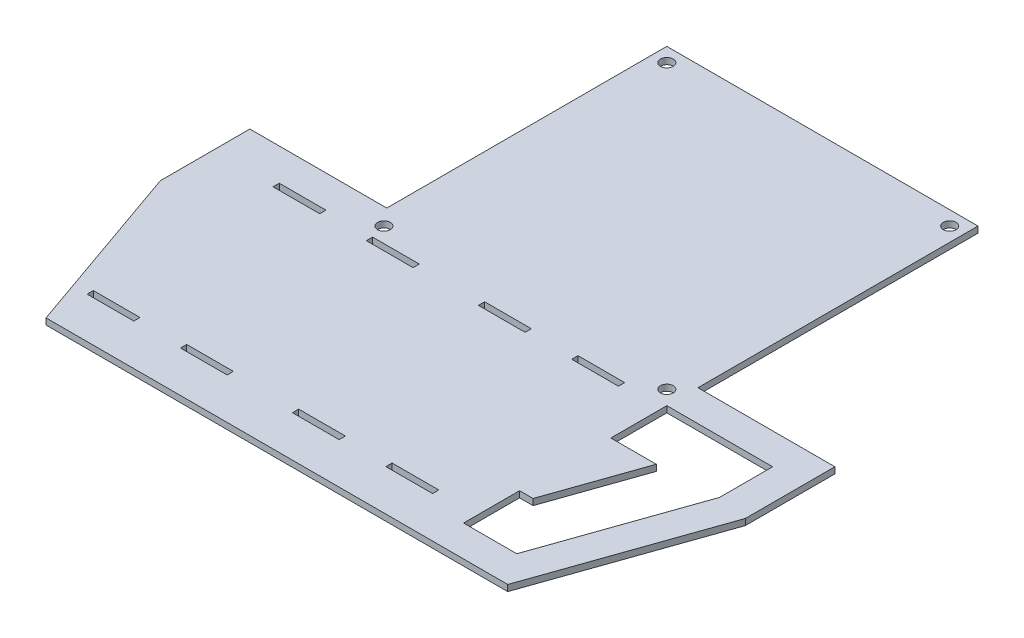
SolidWorks part; units mm, degrees
other "Marca1"
sketch "Croquis6" plane through (-94, 2, 114.9827) normal (0, 1, 0) x (-1, 0, 0)
ref_plane "Alzado" through (0, 0, 0) normal (0, 0, 1) x (1, 0, 0)
ref_plane "Planta" through (0, 0, 0) normal (0, 1, 0) x (1, 0, 0)
ref_plane "Vista lateral" through (0, 0, 0) normal (1, 0, 0) x (0, 0, -1)
sketch "Croquis1" plane through (0, 0, 0) normal (0, 1, 0) x (1, 0, 0)
  line L1 (50, -50) -> (-50, -50) construction
  line L2 (50, -55) -> (50, 50)
  line L3 (50, 50) -> (-50, 50)
  line L4 (-50, -55) -> (-50, 50)
  line L5 (50, -50) -> (-50, 50) construction
  line L6 (50, 50) -> (-50, -50) construction
  line L7 (50, -40) -> (100, -40) construction
  line L8 (74.1939, -125.32) -> (-74.1939, -125.32)
  line L10 (94, -68.7685) -> (94, -40) construction
  line L11 (-50, -55) -> (50, -55) construction
  line L16 (0, 50) -> (0, -114.9827) construction
  line L17 (40, -40) -> (94, -40)
  line L18 (94, -40) -> (94, -68.7685)
  line L19 (-40, -40) -> (-94, -40)
  line L20 (-94, -40) -> (-94, -68.7685)
  line L22 (-50, -40) -> (-100, -40) construction
  line L23 (74.1939, -125.32) -> (94, -68.7685)
  line L24 (-74.1939, -125.32) -> (-94, -68.7685)
  point P0 (0, 0)
  point P7 (0, 0)
  point P10 (0, 0)
  dimension "D1" = 100
  dimension "D2" = 100
  dimension "D3" = 175.32
extrude "Saliente-Extruir1" add sketch "Croquis1" along normal blind 2
sketch "Croquis2" plane through (0, 2, 0) normal (0, 1, 0) x (1, 0, 0)
  line L0 (0, -115) -> (0, 50) construction
  line L1 (50, 50) -> (-50, 50) construction
  line L3 (-50, 0) -> (50, 0) construction
  line L5 (-50, -40) -> (-50, 50) construction
  line L7 (50, -50) -> (-50, -50) construction
  circle A0 centre (-45.45, -45.45) radius 2.05
  circle A1 centre (45.45, -45.45) radius 2.05
  circle A2 centre (-45.45, 45.45) radius 2.05
  circle A3 centre (45.45, 45.45) radius 2.05
  dimension "D1" = 4.1
  dimension "D2" = 4.55
  dimension "D3" = 100
  dimension "D4" = 4.55
  dimension "D5" = 50
  dimension "D6" = 90.9
extrude "Cortar-Extruir1" cut sketch "Croquis2" against normal through all
sketch "Croquis4" plane through (0, 2, 0) normal (0, 1, 0) x (1, 0, 0)
  line L16 (50, -68) -> (64.6015, -68)
  line L17 (64.6015, -68) -> (64.6015, -68)
  line L25 (64.6015, -68) -> (54.3328, -97.32)
  line L26 (54.3328, -97.32) -> (50, -97.32)
  line L27 (67.1006, -115.32) -> (-74.1939, -115.32)
  line L28 (50, -50) -> (84, -50)
  line L29 (84, -50) -> (84, -67.0679)
  line L30 (84, -67.0679) -> (67.1006, -115.32)
  line L31 (67.1006, -115.32) -> (50, -115.32)
  line L32 (50, -50) -> (84, -50)
  line L33 (84, -50) -> (84, -67.0679)
  line L34 (84, -67.0679) -> (67.1006, -115.32)
  line L35 (50, -68) -> (50, -50)
  line L37 (67.1006, -115.32) -> (-74.1939, -115.32) construction
  line L38 (54.3328, -97.32) -> (-74.1939, -97.32) construction
  line L39 (50, -97.32) -> (50, -115.32)
  dimension "D1" = 10
  dimension "D2" = 18
  dimension "D3" = 4.3328
extrude "Cortar-Extruir3" cut sketch "Croquis4" against normal up to next
sketch "Croquis5" plane through (0, 2, 0) normal (0, 1, 0) x (1, 0, 0)
  line L0 (74.1939, -125.32) -> (-74.1939, -125.32) construction
  line L1 (-74.1939, -107.2327) -> (36.8061, -107.2327) construction
  line L2 (-74.1939, -55.2327) -> (36.8061, -55.2327) construction
  line L3 (74.1939, -125.32) -> (-74.1939, -125.32) construction
  line L4 (-74.1939, -107.2327) -> (36.8061, -107.2327) construction
  line L5 (-74.1939, -55.2327) -> (36.8061, -55.2327) construction
  line L6 (45.45, -47.5) -> (-45.45, -47.5) construction
  line L7 (36.8061, -55.2327) -> (36.8061, -47.5) construction
  line L8 (36.8061, -50.3577) -> (21.8061, -50.3577)
  line L9 (36.8061, -50.3577) -> (36.8061, -52.3577)
  line L10 (36.8061, -52.3577) -> (21.8061, -52.3577)
  line L11 (21.8061, -50.3577) -> (21.8061, -52.3577)
  line L12 (36.8061, -51.3577) -> (-74.1865, -51.3577) construction
  line L13 (-18.6939, -55.2327) -> (-18.6939, -47.5) construction
  line L14 (-74.1939, -50.3577) -> (-59.1939, -50.3577)
  line L15 (-74.1939, -50.3577) -> (-74.1939, -52.3577)
  line L16 (-74.1939, -52.3577) -> (-59.1939, -52.3577)
  line L17 (-59.1939, -50.3577) -> (-59.1939, -52.3577)
  line L18 (-44.1939, -50.3577) -> (-29.1939, -50.3577)
  line L19 (-44.1939, -50.3577) -> (-44.1939, -52.3577)
  line L20 (-44.1939, -52.3577) -> (-29.1939, -52.3577)
  line L21 (-29.1939, -50.3577) -> (-29.1939, -52.3577)
  line L22 (-8.1939, -50.3577) -> (6.8061, -50.3577)
  line L23 (-8.1939, -50.3577) -> (-8.1939, -52.3577)
  line L24 (-8.1939, -52.3577) -> (6.8061, -52.3577)
  line L25 (6.8061, -50.3577) -> (6.8061, -52.3577)
  line L26 (-74.1939, -55.2327) -> (-74.1939, -81.2327) construction
  line L27 (36.8061, -81.2327) -> (-74.1939, -81.2327) construction
  line L28 (-74.1939, -110.1077) -> (-59.1939, -110.1077)
  line L29 (-59.1939, -112.1077) -> (-59.1939, -110.1077)
  line L30 (-74.1939, -112.1077) -> (-59.1939, -112.1077)
  line L31 (-74.1939, -112.1077) -> (-74.1939, -110.1077)
  line L32 (-44.1939, -110.1077) -> (-29.1939, -110.1077)
  line L33 (-29.1939, -112.1077) -> (-29.1939, -110.1077)
  line L34 (-44.1939, -112.1077) -> (-29.1939, -112.1077)
  line L35 (-44.1939, -112.1077) -> (-44.1939, -110.1077)
  line L36 (-8.1939, -110.1077) -> (6.8061, -110.1077)
  line L37 (6.8061, -112.1077) -> (6.8061, -110.1077)
  line L38 (-8.1939, -112.1077) -> (6.8061, -112.1077)
  line L39 (-8.1939, -112.1077) -> (-8.1939, -110.1077)
  line L40 (36.8061, -110.1077) -> (21.8061, -110.1077)
  line L41 (21.8061, -112.1077) -> (21.8061, -110.1077)
  line L42 (36.8061, -112.1077) -> (21.8061, -112.1077)
  line L43 (36.8061, -112.1077) -> (36.8061, -110.1077)
  circle A0 centre (45.45, -45.45) radius 2.05 construction
  circle A1 centre (-45.45, -45.45) radius 2.05 construction
  dimension "D1" = 15
  dimension "D2" = 2
  dimension "D3" = 3.875
  dimension "D4" = 15
  dimension "D5" = 2
  dimension "D6" = 15
  dimension "D7" = 2
  dimension "D8" = 15
  dimension "D9" = 2
  dimension "D10" = 15
  dimension "D11" = 15
extrude "Cortar-Extruir4" cut sketch "Croquis5" against normal up to next
